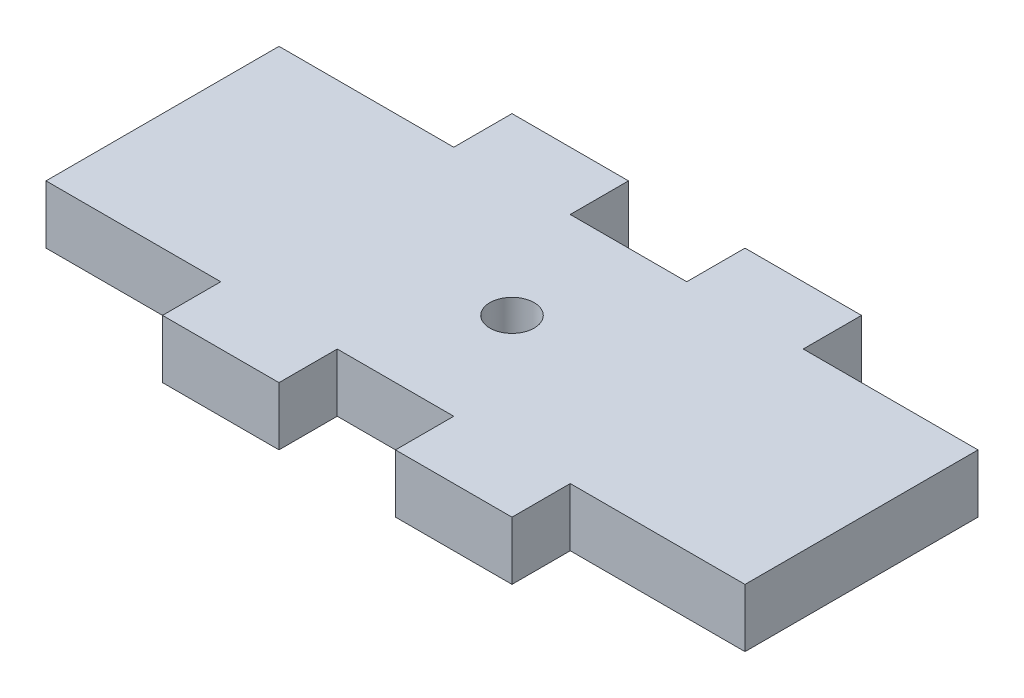
SolidWorks part; units mm, degrees
ref_plane "Front Plane" through (0, 0, 0) normal (0, 0, 1) x (1, 0, 0)
ref_plane "Top Plane" through (0, 0, 0) normal (0, 1, 0) x (1, 0, 0)
ref_plane "Right Plane" through (0, 0, 0) normal (1, 0, 0) x (0, 0, -1)
sketch "Sketch1" plane through (0, 0, 0) normal (0, 1, 0) x (1, 0, 0)
  line L0 (31.75, 0) -> (-25.4, 0) construction
  line L1 (-31.75, -12.7) -> (-25.4, -12.7)
  line L3 (-31.75, 12.7) -> (-25.4, 12.7)
  line L4 (31.75, -12.7) -> (31.75, 12.7)
  line L5 (-31.75, -12.7) -> (31.75, 12.7) construction
  line L6 (-31.75, 12.7) -> (31.75, -12.7) construction
  line L7 (-44.45, 0) -> (-25.4, 0) construction
  line L8 (-31.75, 12.7) -> (-44.45, 12.7)
  line L9 (-12.7, -12.7) -> (0, -12.7)
  line L10 (-31.75, -12.7) -> (-44.45, -12.7)
  line L11 (-44.45, 12.7) -> (-44.45, -12.7)
  line L12 (-6.35, 12.7) -> (-6.35, -12.7) construction
  line L14 (12.7, -12.7) -> (12.7, -19.05)
  line L15 (-12.7, -12.7) -> (-12.7, -19.05)
  line L16 (-12.7, -19.05) -> (-25.4, -19.05)
  line L17 (-25.4, -12.7) -> (-25.4, -19.05)
  line L18 (0, -19.05) -> (12.7, -19.05)
  line L19 (0, -12.7) -> (0, -19.05)
  line L20 (0, 12.7) -> (0, 19.05)
  line L21 (0, 19.05) -> (12.7, 19.05)
  line L22 (-25.4, 12.7) -> (-25.4, 19.05)
  line L23 (-12.7, 19.05) -> (-25.4, 19.05)
  line L24 (-12.7, 12.7) -> (-12.7, 19.05)
  line L25 (12.7, 12.7) -> (12.7, 19.05)
  line L26 (-12.7, 12.7) -> (0, 12.7)
  line L27 (-31.75, 12.7) -> (-25.4, 12.7)
  line L28 (-12.7, 12.7) -> (0, 12.7)
  line L29 (12.7, 12.7) -> (31.75, 12.7)
  line L30 (12.7, 12.7) -> (31.75, 12.7)
  line L31 (12.7, -12.7) -> (31.75, -12.7)
  circle A0 centre (-6.35, 0) radius 2.413
  point P0 (0, 0)
  dimension "D8" = 4.826
  dimension "D1" = 63.5
  dimension "D2" = 25.4
  dimension "D3" = 25.4
  dimension "D4" = 6.35
  dimension "D5" = 12.7
  dimension "D6" = 6.35
  dimension "D7" = 6.35
  dimension "D9" = 12.7
extrude "Boss-Extrude1" add sketch "Sketch1" along normal blind 6.35
